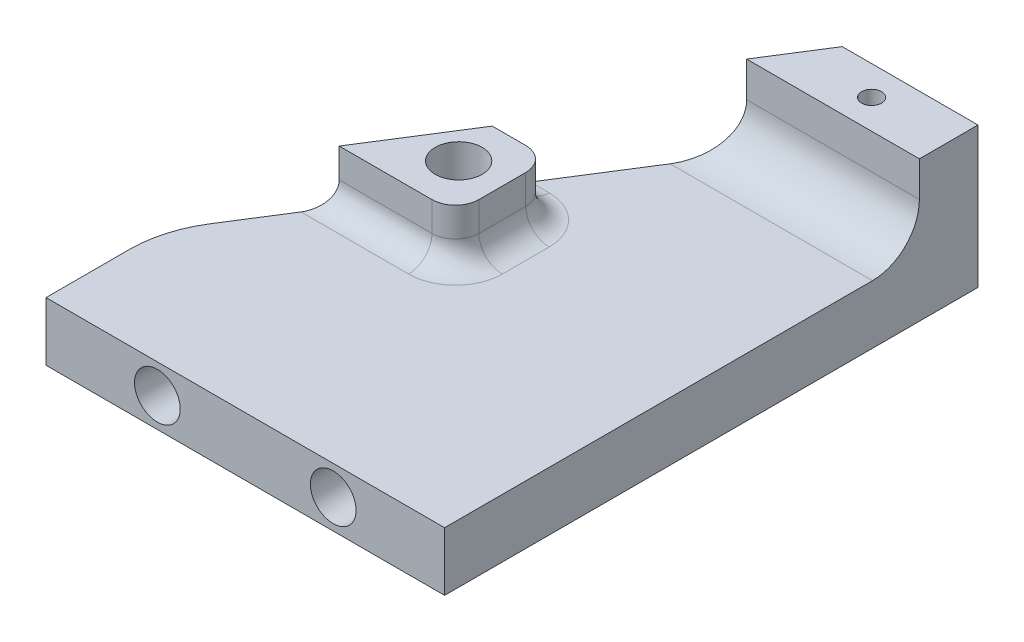
SolidWorks part; units mm, degrees
ref_plane "Front Plane" through (0, 0, 0) normal (0, 0, 1) x (1, 0, 0)
ref_plane "Top Plane" through (0, 0, 0) normal (0, 1, 0) x (1, 0, 0)
ref_plane "Right Plane" through (0, 0, 0) normal (1, 0, 0) x (0, 0, -1)
sketch "Sketch1" plane through (0, 0, 0) normal (0, 0, 1) x (1, 0, 0)
  line L0 (-9.3898, 4.5) -> (24.6102, 4.5)
  line L1 (-9.3898, -24.5) -> (24.6102, -24.5)
  line L7 (24.6102, 4.5) -> (24.6102, -24.5)
  line L8 (-9.3898, 4.5) -> (-9.3898, -24.5)
  circle A1 centre (15.0102, 0) radius 1.4
  circle A3 centre (15.0102, -20) radius 1.4
  circle A4 centre (0.0102, 0) radius 1.5
  circle A5 centre (0.0102, -20) radius 1.5
extrude "Boss-Extrude1" add sketch "Sketch1" along normal blind 5
sketch "Sketch2" plane through (0, -24.5, 0) normal (0, -1, 0) x (1, 0, 0)
  line L0 (-9.3898, -10) -> (-9.3898, 5)
  line L1 (-9.3898, 5) -> (24.6102, 5)
  line L2 (24.6102, -48) -> (14.6102, -48)
  line L3 (-9.3898, -10) -> (14.6102, -48)
  line L4 (24.6102, 5) -> (24.6102, -48)
extrude "Boss-Extrude2" add sketch "Sketch2" along normal blind 5
sketch "Sketch3" plane through (0, -24.5, 0) normal (0, 1, 0) x (1, 0, 0)
  line L0 (24.6102, 40.5) -> (9.8734, 40.5)
  line L1 (24.6102, 48) -> (24.6102, 0) construction
  line L2 (-9.3898, 10) -> (14.6102, 48) construction
  line L3 (24.6102, 45.5) -> (13.0313, 45.5)
  line L4 (13.0313, 45.5) -> (9.8734, 40.5)
  line L7 (24.6102, 45.5) -> (24.6102, 40.5)
  circle A0 centre (18.0313, 43) radius 0.85
extrude "Boss-Extrude3" add sketch "Sketch3" along normal blind 7
sketch "Sketch6" plane through (0, -24.5, 0) normal (0, 1, 0) x (1, 0, 0)
  line L0 (13.0313, 45.5) -> (24.6102, 45.5)
  line L1 (24.6102, 45.5) -> (24.6102, 48)
  line L2 (24.6102, 48) -> (14.6102, 48)
  line L3 (14.6102, 48) -> (13.0313, 45.5)
extrude "Cut-Extrude2" cut sketch "Sketch6" against normal blind 5
fillet "Fillet1" radius 4 1 edges at (17.2418, -24.5, -40.5)
sketch "Sketch7" plane through (-9.3898, 0, 0) normal (-1, 0, 0) x (0, 0, 1)
  line L0 (5, -29.5) -> (-10, -29.5) construction
  line L1 (0, -29.5) -> (5, -29.5)
  line L2 (0, -29.5) -> (0, 4.5)
  line L3 (0, 4.5) -> (5, 4.5)
  line L4 (5, -29.5) -> (5, 4.5)
extrude "Cut-Extrude3" cut sketch "Sketch7" against normal blind 44
sketch "Sketch8" plane through (0, 0, 0) normal (0, 0, 1) x (1, 0, 0)
  circle A0 centre (15.1102, -27) radius 1.95
  circle A1 centre (0.1102, -27) radius 1.95
extrude "Cut-Extrude4" cut sketch "Sketch8" against normal blind 6
fillet "Fillet2" radius 10 1 edges at (-9.3898, -27, -10)
sketch "Sketch9" plane through (0, -24.5, 0) normal (0, 1, 0) x (1, 0, 0)
  circle A0 centre (2.6102, 23.2) radius 2
sketch "Sketch11" plane through (0, -24.5, 0) normal (0, 1, 0) x (1, 0, 0)
  line L0 (1.4734, 27.2) -> (4.3326, 27.2)
  line L1 (-7.8447, 12.4464) -> (7.347, 36.5) construction
  line L2 (6.3326, 25.2) -> (6.3326, 21.2)
  line L3 (4.3326, 19.2) -> (-3.5793, 19.2)
  line L4 (-3.5793, 19.2) -> (1.4734, 27.2)
  arc A0 (6.3326, 21.2) -> (4.3326, 19.2) centre (4.3326, 21.2) cw
  arc A1 (4.3326, 27.2) -> (6.3326, 25.2) centre (4.3326, 25.2) cw
  dimension "D1" = 2
extrude "Boss-Extrude4" add sketch "Sketch11" along normal blind 4.5
extrude "Cut-Extrude5" cut sketch "Sketch9" against normal blind 5 from surface at 4.5 starting at face at (3.3422, -20, -23.2)
fillet "Fillet3" radius 2 5 edges at (0.3767, -24.5, -19.2) (2.903, -24.5, -27.2) (5.7468, -24.5, -26.6142) (5.7468, -24.5, -19.7858) (6.3326, -24.5, -23.2)
